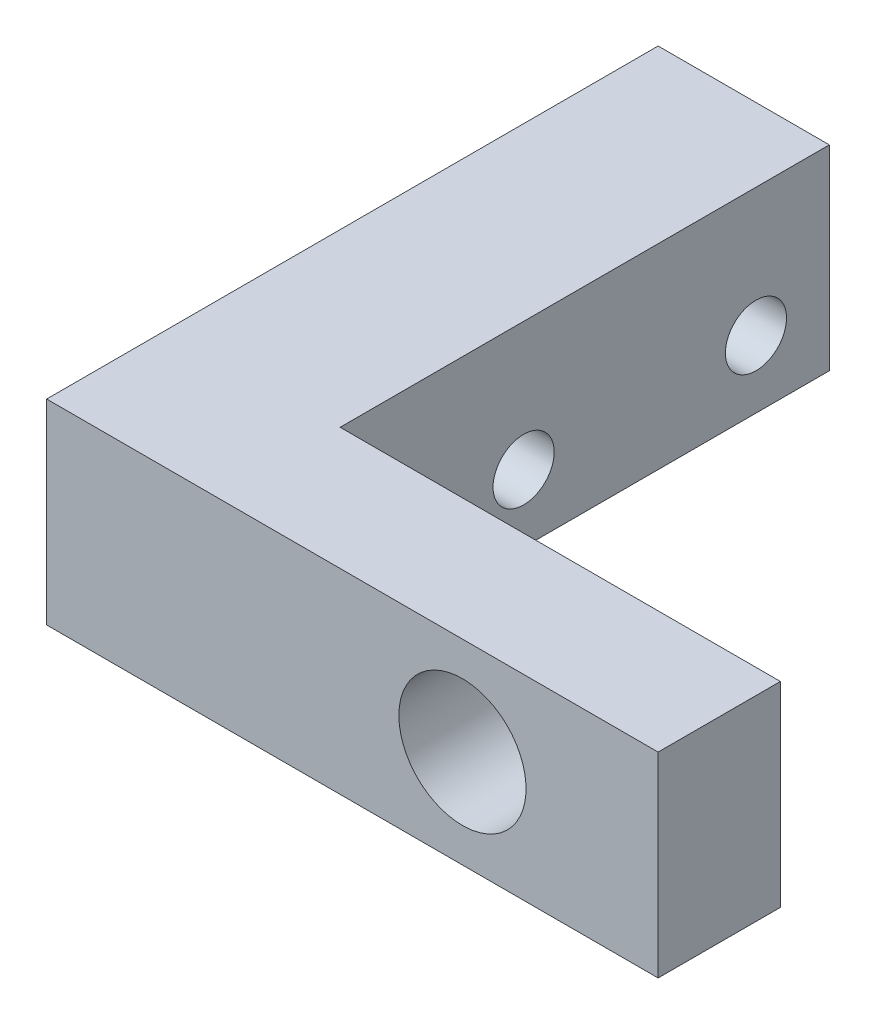
SolidWorks part; units mm, degrees
material "ABS"
ref_plane "Front Plane" through (0, 0, 0) normal (0, 0, 1) x (1, 0, 0)
ref_plane "Top Plane" through (0, 0, 0) normal (0, 1, 0) x (1, 0, 0)
ref_plane "Right Plane" through (0, 0, 0) normal (1, 0, 0) x (0, 0, -1)
sketch "Sketch1" plane through (0, 0, 0) normal (0, 1, 0) x (1, 0, 0)
  line L0 (0, 0) -> (0, 25)
  line L1 (0, 25) -> (7, 25)
  line L2 (7, 25) -> (7, 5)
  line L3 (7, 5) -> (25, 5)
  line L4 (25, 5) -> (25, 0)
  line L5 (25, 0) -> (0, 0)
  dimension "D1" = 25
  dimension "D2" = 25
  dimension "D3" = 5
  dimension "D4" = 7
extrude "Boss-Extrude1" add sketch "Sketch1" along normal blind 8
sketch "Sketch2" plane through (0, 0, 0) normal (-1, 0, 0) x (0, 0, 1)
  line L0 (-25, 8) -> (-25, 0) construction
  line L2 (-5, 0) -> (-25, 0) construction
  circle A0 centre (-22, 2.75) radius 1.25
  circle A1 centre (-12.5, 2.75) radius 1.25
  dimension "D2" = 2.5
  dimension "D3" = 3
  dimension "D4" = 2.75
  dimension "D1" = 9.5
extrude "Cut-Extrude1" cut sketch "Sketch2" against normal up to next
sketch "Sketch4" plane through (0, 0, -5) normal (0, 0, -1) x (-1, 0, 0)
  line L0 (-17, 8) -> (-17, 0) construction
  line L1 (-25, 8) -> (-7, 8) construction
  line L2 (-25, 0) -> (-7, 0) construction
  line L6 (-7, 8) -> (-7, 0) construction
  circle A0 centre (-17, 4) radius 2.6
  dimension "D1" = 5.2
  dimension "D2" = 10
extrude "Cut-Extrude2" cut sketch "Sketch4" against normal up to next
